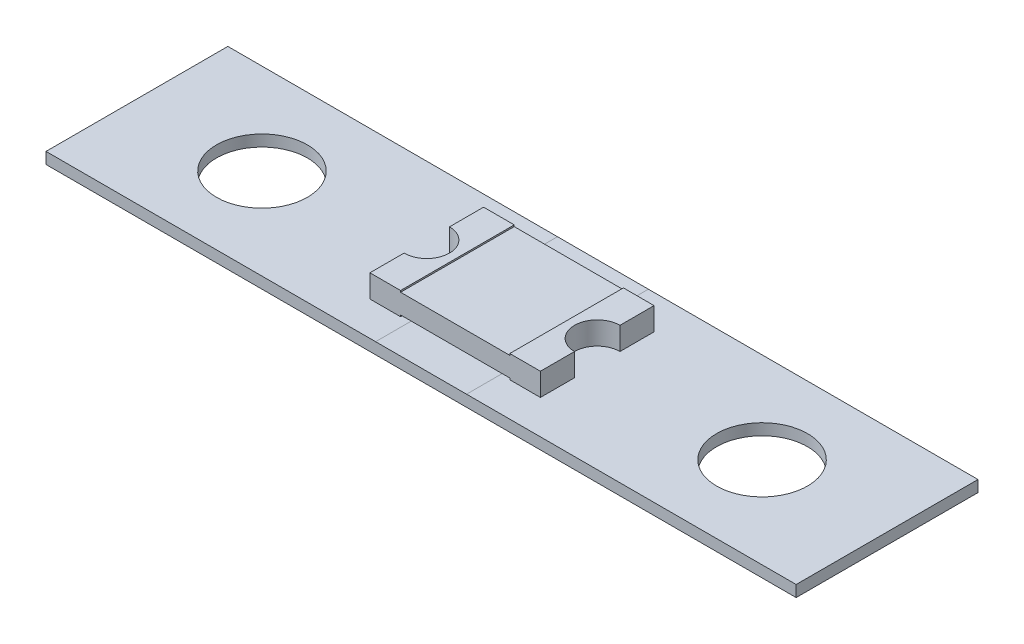
SolidWorks part; units mm, degrees
ref_plane "Front Plane" through (0, 0, 0) normal (0, 0, 1) x (1, 0, 0)
ref_plane "Top Plane" through (0, 0, 0) normal (0, 1, 0) x (1, 0, 0)
ref_plane "Right Plane" through (0, 0, 0) normal (1, 0, 0) x (0, 0, -1)
sketch "Sketch1" plane through (0, 0, 0) normal (0, 1, 0) x (1, 0, 0)
  line L0 (-44.2539, 0) -> (44.2539, 0) construction
  line L1 (-16.5, -4) -> (16.5, -4)
  line L2 (-16.5, -4) -> (-16.5, 4)
  line L3 (-16.5, 4) -> (16.5, 4)
  line L4 (16.5, -4) -> (16.5, 4)
  line L5 (-16.5, -4) -> (16.5, 4) construction
  line L6 (-16.5, 4) -> (16.5, -4) construction
  line L7 (0, -44.7868) -> (0, 44.7868) construction
  circle A0 centre (-11, 0) radius 2
  circle A1 centre (11, 0) radius 2
  point P0 (0, 0)
  dimension "D3" = 4
  dimension "D4" = 22
  dimension "D5" = 11
  dimension "D1" = 8
  dimension "D2" = 33
extrude "Boss-Extrude1" add sketch "Sketch1" along normal blind 0.5 contours L1 L4 L3 L2
sketch "Sketch3" plane through (0, 0.5, 0) normal (0, 1, 0) x (1, 0, 0)
  line L1 (-3.75, -2.5) -> (3.75, -2.5)
  line L2 (-3.75, -2.5) -> (-3.75, 2.5)
  line L3 (-3.75, 2.5) -> (3.75, 2.5)
  line L4 (3.75, -2.5) -> (3.75, 2.5)
  line L5 (-3.75, -2.5) -> (3.75, 2.5) construction
  line L6 (-3.75, 2.5) -> (3.75, -2.5) construction
  circle A0 centre (-3.75, 0) radius 1
  circle A1 centre (3.75, 0) radius 1
  point P0 (0, 0)
  dimension "D3" = 2
  dimension "D4" = 2
  dimension "D1" = 5
  dimension "D2" = 7.5
extrude "Boss-Extrude2" add sketch "Sketch3" along normal blind 1 separate body contours A1 L4 L3 L2 A0 L1
sketch "Sketch4" plane through (0, 0, 2.5) normal (0, 0, 1) x (1, 0, 0)
  line L0 (-3.75, 1.5) -> (3.75, 1.5) construction
  line L1 (-2.4018, 1.5) -> (2.4018, 1.5)
  line L2 (-2.4018, 1.5) -> (-2.4018, 1.4321)
  line L3 (-2.4018, 1.4321) -> (2.4018, 1.4321)
  line L4 (2.4018, 1.5) -> (2.4018, 1.4321)
  line L6 (-2.4018, 0.5) -> (2.4018, 0.5)
  line L7 (-2.4018, 0.5) -> (-2.4018, 0.5679)
  line L8 (-2.4018, 0.5679) -> (2.4018, 0.5679)
  line L9 (2.4018, 0.5) -> (2.4018, 0.5679)
  line L10 (0, 0.5679) -> (0, 0) construction
  line L11 (-3.75, 0.5) -> (3.75, 0.5) construction
extrude "Cut-Extrude1" cut sketch "Sketch4" against normal through all
sketch "Sketch5" plane through (0, 0.5, 0) normal (0, 1, 0) x (1, 0, 0)
  line L0 (16.5, 4) -> (-16.5, 4) construction
  line L1 (-2, -4) -> (2, -4)
  line L2 (-2, -4) -> (-2, 4)
  line L3 (-2, 4) -> (2, 4)
  line L4 (2, -4) -> (2, 4)
  line L5 (-2, -4) -> (2, 4) construction
  line L6 (-2, 4) -> (2, -4) construction
  point P0 (0, 0)
  dimension "D1" = 4
split line "Split Line1"
